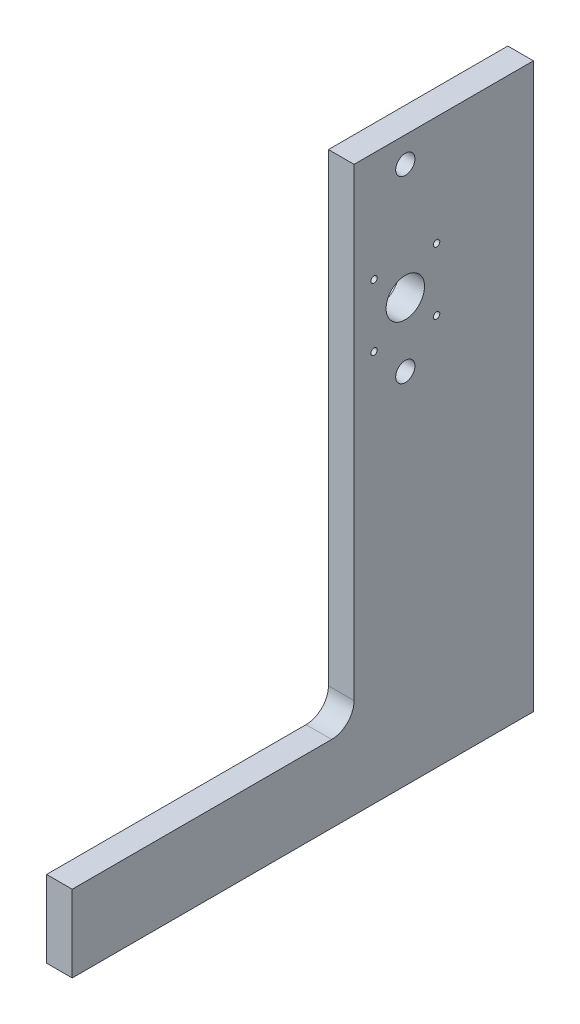
SolidWorks part; units mm, degrees
ref_plane "Front Plane" through (0, 0, 0) normal (0, 0, 1) x (1, 0, 0)
ref_plane "Top Plane" through (0, 0, 0) normal (0, 1, 0) x (1, 0, 0)
ref_plane "Right Plane" through (0, 0, 0) normal (1, 0, 0) x (0, 0, -1)
sketch "Sketch1" plane through (0, 0, 0) normal (1, 0, 0) x (0, 0, -1)
  line L0 (0, 0) -> (0, 38.1)
  line L1 (0, 0) -> (228.6, 0)
  line L2 (228.6, 0) -> (228.6, 279.4)
  line L3 (228.6, 279.4) -> (139.7, 279.4)
  line L4 (139.7, 279.4) -> (139.7, 49.2125)
  line L5 (128.5875, 38.1) -> (0, 38.1)
  arc A0 (139.7, 49.2125) -> (128.5875, 38.1) centre (128.5875, 49.2125) cw
  circle A1 centre (165.1, 266.7) radius 4.7625
  circle A2 centre (165.1, 177.8) radius 4.7625
  circle A3 centre (165.1, 209.55) radius 9.525
  circle A4 centre (180.6, 225.05) radius 1.5875
  circle A5 centre (149.612, 225.05) radius 1.5875
  circle A6 centre (180.6, 194.062) radius 1.5875
  circle A7 centre (149.612, 194.062) radius 1.5875
  dimension "D1" = 11.1125
  dimension "D2" = 2
  dimension "D3" = 2
  dimension "D4" = 2
extrude "Boss-Extrude1" add sketch "Sketch1" along normal blind 12.7
